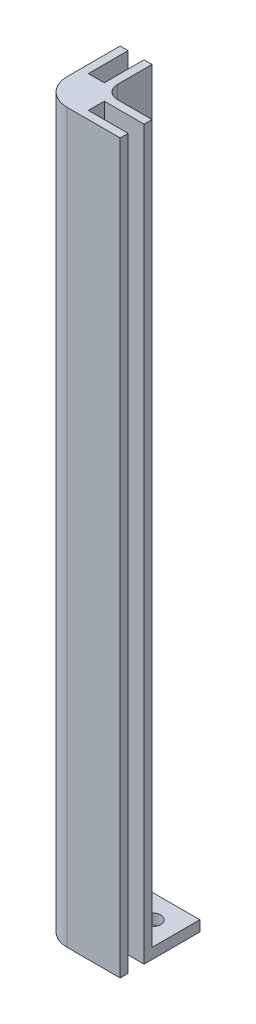
SolidWorks part; units mm, degrees
material "ABS"
ref_plane "Front Plane" through (0, 0, 0) normal (0, 0, 1) x (1, 0, 0)
ref_plane "Top Plane" through (0, 0, 0) normal (0, 1, 0) x (1, 0, 0)
ref_plane "Right Plane" through (0, 0, 0) normal (1, 0, 0) x (0, 0, -1)
sketch "Sketch4" plane through (0, 0, 0) normal (0, 1, 0) x (1, 0, 0)
  line L0 (-7.5, -7.5) -> (7.5, -7.5)
  line L1 (7.5, -7.5) -> (7.5, -6)
  line L2 (7.5, -6) -> (0, -6)
  line L3 (0, -6) -> (0, -3)
  line L4 (0, -3) -> (7.5, -3)
  line L5 (7.5, -3) -> (7.5, -1.5)
  line L6 (7.5, -1.5) -> (-1.5, -1.5)
  line L7 (-7.5, -7.5) -> (-7.5, 7.5)
  line L8 (-7.5, 7.5) -> (-6, 7.5)
  line L9 (-3, 7.5) -> (-1.5, 7.5)
  line L10 (-1.5, 7.5) -> (-1.5, -1.5)
  line L11 (-6, 7.5) -> (-6, 0)
  line L12 (-6, 0) -> (-3, 0)
  line L13 (-3, 0) -> (-3, 7.5)
  point P14 (0, -7.5)
  dimension "D1" = 15
  dimension "D2" = 1.5
  dimension "D3" = 9
  dimension "D4" = 3
  dimension "D5" = 7.5
  dimension "D6" = 7.5
  dimension "D7" = 7.5
  dimension "D8" = 7.5
  dimension "D9" = 6
extrude "Boss-Extrude1" add sketch "Sketch4" along normal blind 135
sketch "Sketch6" plane through (0, 0, 0) normal (0, -1, 0) x (1, 0, 0)
  line L0 (-7.5, 7.5) -> (7.5, 7.5)
  line L2 (-1.5, -7.5) -> (-7.5, -7.5)
  line L3 (-7.5, -7.5) -> (-7.5, 7.5)
  line L5 (7.5, 7.5) -> (7.5, 6)
  line L6 (7.5, 6) -> (0, 6)
  line L7 (0, 6) -> (0, 3)
  line L8 (0, 3) -> (7.5, 3)
  line L9 (7.5, 3) -> (7.5, 1.5)
  line L10 (7.5, 1.5) -> (-1.5, 1.5) construction
  line L11 (3, 1.5) -> (3, -3) construction
  line L12 (-1.5, -7.5) -> (-3, -7.5)
  line L13 (-3, -7.5) -> (-3, 0)
  line L14 (-3, 0) -> (-6, 0)
  line L15 (-6, 0) -> (-6, -7.5)
  line L16 (-6, -7.5) -> (-7.5, -7.5)
  line L17 (7.5, 1.5) -> (7.5, -7.5)
  line L18 (7.5, -7.5) -> (-1.5, -7.5)
  circle A0 centre (3, -3) radius 1.6
  dimension "D1" = 3.2
extrude "Boss-Extrude2" add sketch "Sketch6" along normal blind 2
fillet "Fillet3" radius 5 1 edges at (-7.5, 66.5, 7.5)
fillet "Fillet4" radius 2.5 1 edges at (-1.5, 67.5, 1.5)
